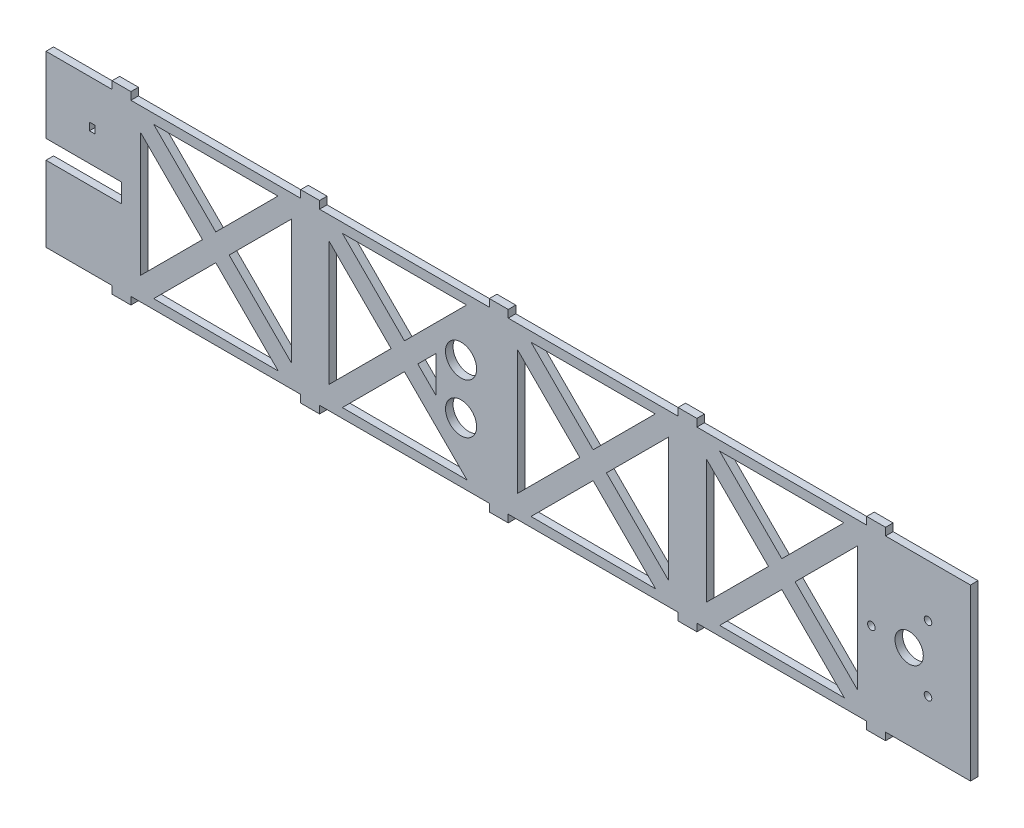
SolidWorks part; units mm, degrees
ref_plane "Piano frontale" through (0, 0, 0) normal (0, 0, 1) x (1, 0, 0)
ref_plane "Piano superiore" through (0, 0, 0) normal (0, 1, 0) x (1, 0, 0)
ref_plane "Piano destro" through (0, 0, 0) normal (1, 0, 0) x (0, 0, -1)
sketch "Schizzo1" plane through (0, 0, 0) normal (0, 0, 1) x (1, 0, 0)
  line L0 (0, 50) -> (0, 90)
  line L1 (0, 0) -> (35, 0)
  line L2 (0, 0) -> (0, 40)
  line L3 (0, 90) -> (35, 90)
  line L4 (490, 0) -> (490, 90)
  line L5 (0, 40) -> (40, 40)
  line L6 (490, 45) -> (0, 45) construction
  line L7 (0, 50) -> (40, 50)
  line L8 (40, 40) -> (40, 50)
  line L9 (45, 90) -> (45, 0) construction
  line L10 (135, 90) -> (135, 0) construction
  line L11 (45, 90) -> (135, 0) construction
  line L12 (45, 0) -> (135, 0) construction
  line L13 (135, 90) -> (45, 0) construction
  line L14 (50, 77.9289) -> (50, 12.0711)
  line L15 (130, 77.9289) -> (130, 12.0711)
  line L16 (45, 0) -> (50, 0) construction
  line L17 (50, 77.9289) -> (82.9289, 45)
  line L18 (57.0711, 85) -> (90, 52.0711)
  line L19 (122.9289, 85) -> (90, 52.0711)
  line L20 (130, 77.9289) -> (97.0711, 45)
  line L21 (57.0711, 85) -> (122.9289, 85)
  line L22 (123.1448, 4.7841) -> (57.0772, 5.0061)
  line L23 (131.4645, 93.5355) -> (41.4645, 3.5355) construction
  line L24 (138.5355, 86.4645) -> (48.5355, -3.5355) construction
  line L25 (220, 58.25) -> (220, 31.75) construction
  line L26 (41.4645, 86.4645) -> (131.4645, -3.5355) construction
  line L27 (130, 90) -> (130, 0) construction
  line L28 (48.5355, 93.5355) -> (138.5355, 3.5355) construction
  line L29 (90, 37.9289) -> (123.1448, 4.7841)
  line L30 (97.0711, 45) -> (130, 12.0711)
  line L31 (82.9289, 45) -> (50, 12.0711)
  line L32 (90, 37.9289) -> (57.0772, 5.0061)
  line L33 (150, 77.9289) -> (150, 12.0711)
  line L34 (190, 37.9289) -> (206.75, 54.6789) construction
  line L35 (150, 77.9289) -> (182.9289, 45)
  line L36 (157.0711, 85) -> (190, 52.0711)
  line L37 (222.9289, 85) -> (190, 52.0711)
  line L38 (190, 52.0711) -> (206.75, 35.3211) construction
  line L39 (157.0711, 85) -> (222.9289, 85)
  line L40 (223.1448, 4.7841) -> (157.0772, 5.0061)
  line L41 (190, 37.9289) -> (223.1448, 4.7841)
  line L42 (206.75, 54.6789) -> (206.75, 35.3211) construction
  line L43 (182.9289, 45) -> (150, 12.0711)
  line L44 (190, 37.9289) -> (157.0772, 5.0061)
  line L45 (445, 94) -> (445, 90)
  line L46 (250, 77.9289) -> (250, 12.0711)
  line L47 (330, 77.9289) -> (330, 12.0711)
  line L48 (250, 77.9289) -> (282.9289, 45)
  line L49 (257.0711, 85) -> (290, 52.0711)
  line L50 (322.9289, 85) -> (290, 52.0711)
  line L51 (330, 77.9289) -> (297.0711, 45)
  line L52 (257.0711, 85) -> (322.9289, 85)
  line L53 (323.1448, 4.7841) -> (257.0772, 5.0061)
  line L54 (290, 37.9289) -> (323.1448, 4.7841)
  line L55 (297.0711, 45) -> (330, 12.0711)
  line L56 (282.9289, 45) -> (250, 12.0711)
  line L57 (290, 37.9289) -> (257.0772, 5.0061)
  line L58 (350, 77.9289) -> (350, 12.0711)
  line L59 (430, 77.9289) -> (430, 12.0711)
  line L60 (350, 77.9289) -> (382.9289, 45)
  line L61 (357.0711, 85) -> (390, 52.0711)
  line L62 (422.9289, 85) -> (390, 52.0711)
  line L63 (430, 77.9289) -> (397.0711, 45)
  line L64 (435, 94) -> (445, 94)
  line L65 (357.0711, 85) -> (422.9289, 85)
  line L66 (423.1448, 4.7841) -> (357.0772, 5.0061)
  line L67 (390, 37.9289) -> (423.1448, 4.7841)
  line L68 (397.0711, 45) -> (430, 12.0711)
  line L69 (382.9289, 45) -> (350, 12.0711)
  line L70 (390, 37.9289) -> (357.0772, 5.0061)
  line L71 (50, 77.9289) -> (150, 77.9289) construction
  line L72 (23, 65) -> (26, 65)
  line L73 (23, 65) -> (23, 69)
  line L74 (23, 69) -> (26, 69)
  line L75 (26, 65) -> (26, 69)
  line L76 (206.75, 54.6789) -> (197.0711, 45)
  line L77 (206.75, 35.3211) -> (197.0711, 45)
  line L78 (206.75, 54.6789) -> (206.75, 35.3211)
  line L83 (435, 90) -> (435, 94)
  line L85 (35, 0) -> (35, -4)
  line L86 (35, -4) -> (45, -4)
  line L87 (45, -4) -> (45, 0)
  line L88 (135, 0) -> (135, -4)
  line L89 (135, -4) -> (145, -4)
  line L90 (145, -4) -> (145, 0)
  line L91 (235, 0) -> (235, -4)
  line L92 (235, -4) -> (245, -4)
  line L93 (245, -4) -> (245, 0)
  line L94 (335, 0) -> (335, -4)
  line L95 (335, -4) -> (345, -4)
  line L96 (345, -4) -> (345, 0)
  line L97 (435, 0) -> (435, -4)
  line L98 (435, -4) -> (445, -4)
  line L99 (445, -4) -> (445, 0)
  line L100 (445, 0) -> (490, 0)
  line L101 (345, 0) -> (435, 0)
  line L102 (245, 0) -> (335, 0)
  line L103 (145, 0) -> (235, 0)
  line L104 (45, 0) -> (135, 0)
  line L108 (345, 94) -> (345, 90)
  line L109 (335, 94) -> (345, 94)
  line L110 (335, 90) -> (335, 94)
  line L111 (245, 94) -> (245, 90)
  line L112 (235, 94) -> (245, 94)
  line L113 (235, 90) -> (235, 94)
  line L114 (145, 94) -> (145, 90)
  line L115 (135, 94) -> (145, 94)
  line L116 (135, 90) -> (135, 94)
  line L117 (45, 94) -> (45, 90)
  line L118 (35, 94) -> (45, 94)
  line L119 (35, 90) -> (35, 94)
  line L120 (45, 90) -> (135, 90)
  line L121 (145, 90) -> (235, 90)
  line L122 (245, 90) -> (335, 90)
  line L123 (345, 90) -> (435, 90)
  line L124 (445, 90) -> (490, 90)
  line L125 (467.5, 27.6795) -> (457.5, 45) construction
  line L126 (467.5, 62.3205) -> (457.5, 45) construction
  line L127 (230, 77.9289) -> (197.0711, 45) [skipped]
  line L128 (197.0711, 45) -> (230, 12.0711) [skipped]
  line L129 (230, 77.9289) -> (230, 12.0711) [skipped]
  circle A0 centre (457.5, 45) radius 7.5
  circle A1 centre (437.5, 45) radius 2
  circle A2 centre (467.5, 27.6795) radius 2
  circle A3 centre (467.5, 62.3205) radius 2
  circle A4 centre (220, 58.25) radius 8.25
  circle A5 centre (220, 31.75) radius 8.25
  dimension "D19" = 15
  dimension "D20" = 4
  dimension "D22" = 4
  dimension "D30" = 16.5
  dimension "D2" = 490
  dimension "D3" = 40
  dimension "D4" = 3
  dimension "D5" = 10
  dimension "D6" = 5
  dimension "D7" = 40
  dimension "D8" = 5
  dimension "D9" = 5
  dimension "D10" = 5
  dimension "D11" = 32.5
  dimension "D12" = 35
  dimension "D13" = 10
  dimension "D14" = 5
  dimension "D15" = 4
  dimension "D16" = 4
  dimension "D17" = 4
  dimension "D18" = 4
  dimension "D21" = 20
  dimension "D23" = 20
  dimension "D24" = 4
  dimension "D25" = 100
  dimension "D26" = 4
  dimension "D27" = 4
  dimension "D28" = 23
  dimension "D29" = 15
  dimension "D31" = 13.25
  dimension "D32" = 30
  dimension "D33" = 43.25
  dimension "D34" = 490
  dimension "D35" = 45
extrude "Estrusione-Estrusione1" add sketch "Schizzo1" along normal blind 4
